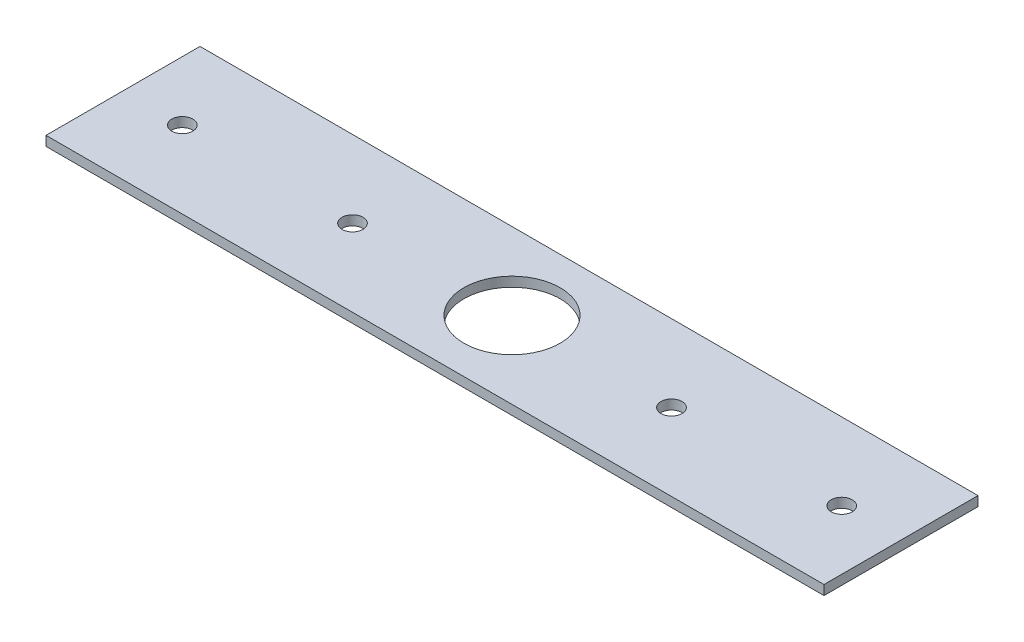
SolidWorks part; units mm, degrees
ref_plane "Front Plane" through (0, 0, 0) normal (0, 0, 1) x (1, 0, 0)
ref_plane "Top Plane" through (0, 0, 0) normal (0, 1, 0) x (1, 0, 0)
ref_plane "Right Plane" through (0, 0, 0) normal (1, 0, 0) x (0, 0, -1)
sketch "Sketch1" plane through (0, 0, 0) normal (0, 1, 0) x (1, 0, 0)
  line L0 (-41.296, 14.2657) -> (39.524, 14.2657) construction
  line L1 (-41.296, 22.2657) -> (39.524, 22.2657)
  line L2 (-41.296, 22.2657) -> (-41.296, 6.2657)
  line L3 (-41.296, 6.2657) -> (39.524, 6.2657)
  line L4 (39.524, 22.2657) -> (39.524, 6.2657)
  line L6 (-0.886, 22.2657) -> (-0.886, 6.2657) construction
  circle A1 centre (-35.136, 14.2657) radius 1.09
  circle A2 centre (33.364, 14.2657) radius 1.09
  circle A3 centre (-17.456, 14.2657) radius 1.09
  circle A4 centre (15.684, 14.2657) radius 1.09
  circle A5 centre (-0.886, 14.2657) radius 5
  dimension "D3" = 6.16
  dimension "D4" = 2.18
  dimension "D5" = 2.18
  dimension "D6" = 17.68
  dimension "D7" = 10
  dimension "D8" = 2.18
  dimension "D9" = 2.18
  dimension "D10" = 17.68
  dimension "D11" = 6.16
  dimension "D1" = 80.82
  dimension "D2" = 16
extrude "Boss-Extrude1" add sketch "Sketch1" along normal blind 1
